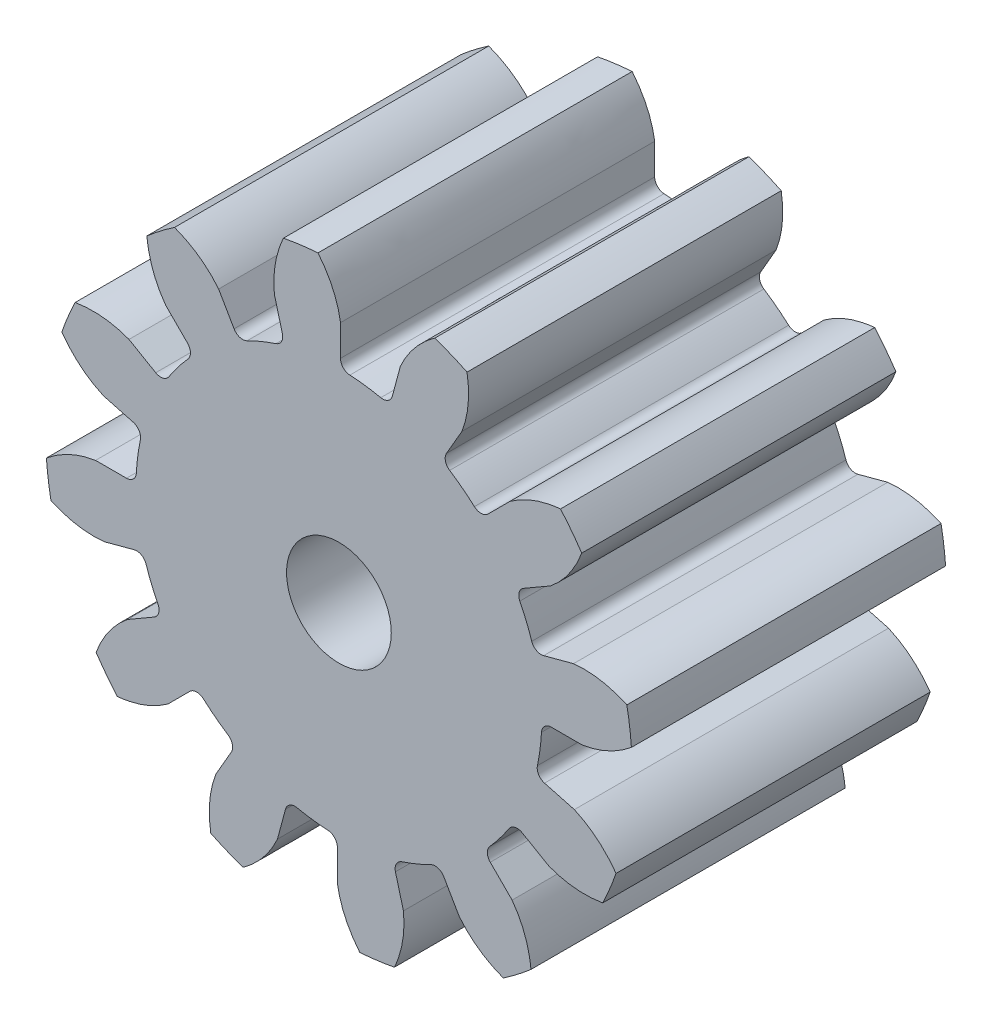
SolidWorks part; units mm, degrees
ref_plane "Front" through (0, 0, 0) normal (0, 0, 1) x (1, 0, 0)
ref_plane "Top" through (0, 0, 0) normal (0, 1, 0) x (1, 0, 0)
ref_plane "Right" through (0, 0, 0) normal (1, 0, 0) x (0, 0, -1)
sketch "Sketch1" plane through (0, 0, 0) normal (0, 0, 1) x (1, 0, 0)
  line L0 (-152.4, 0) -> (152.4, 0) construction
  circle A0 centre (0, 0) radius 8.89
  circle A1 centre (0, 0) radius 7.62 construction
  circle A3 centre (0, 0) radius 6.1506 construction
  dimension "D1" = 1.4694
  dimension "OD" = 17.78
  dimension "Ptich Dia" = 15.24
  dimension "D2" = 2.7394
  dimension "Root Dia" = 12.3012
  dimension "D3" = 1.27
  dimension "Number of Teeth" = 304.8
extrude "Boss-Extrude1" add sketch "Sketch1" against normal blind 9.525
sketch "Sketch3" plane through (0, 0, 0) normal (0, 0, 1) x (1, 0, 0)
  line L0 (0, 0) -> (0, 8.89) construction
  line L1 (-1.8471, 7.1423) -> (0, 7.62)
  line L2 (-9.5921, 7.62) -> (9.5921, 7.62) construction
  line L3 (-9.2865, 5.2183) -> (9.2865, 10.0217) construction
  line L4 (-1.8471, 7.1423) -> (0, 0) construction
  line L5 (-4.563, 5.7968) -> (0, 0) construction
  line L6 (-4.563, 5.7968) -> (-0.6452, 8.8807) construction
  line L7 (-1.288, 7.264) -> (0, 0) construction
  line L8 (-1.288, 7.264) -> (0.027, 7.4971) construction
  arc A0 (-1.8471, 7.1423) -> (-4.563, 5.7968) centre (0, 0) ccw
  circle A1 centre (0, 0) radius 7.62 construction
  circle A2 centre (0, 0) radius 7.3773 construction
  arc A3 (-1.8471, 7.1423) -> (-1.288, 7.264) centre (0, 0) cw
  circle A4 centre (0, 0) radius 8.89 construction
  point P6 (0, 7.62)
  dimension "D1" = 1.9079
  dimension "Pressure Angle" = 14.5
  dimension "D2" = 3.0526
  dimension "D3" = 4.9859
  dimension "D4" = 0.5724
  dimension "D5" = 1.3355
sketch "Sketch4" plane through (0, 0, 0) normal (0, 0, 1) x (1, 0, 0)
  line L0 (0, 0) -> (0.9861, 7.4902) construction
  line L1 (0.0483, 7.3771) -> (0.0483, 6.1504)
  line L2 (0, 7.62) -> (1.9722, 7.3604) construction
  line L3 (1.8627, 7.1383) -> (1.5452, 5.9534)
  line L4 (0.0483, 6.1504) -> (0, 0) construction
  line L5 (0, 0) -> (0, 8.89) construction
  line L6 (-4.563, 5.7968) -> (-0.6452, 8.8807) construction
  line L7 (-4.563, 5.7968) -> (-0.6452, 8.8807) construction
  arc A0 (1.5452, 5.9534) -> (0.0483, 6.1504) centre (0, 0) ccw
  arc A1 (0, 7.62) -> (1.9722, 7.3604) centre (0, 0) cw construction
  circle A2 centre (0, 0) radius 7.62 construction
  circle A3 centre (0, 0) radius 7.3773 construction
  circle A4 centre (0, 0) radius 6.1506 construction
  arc A5 (2.9218, 8.4111) -> (-0.6452, 8.8807) centre (0, 0) ccw
  spline S0 degree 2 poles (-0.6452, 8.8807) (-0.0806, 8.1997) (0.0483, 7.3771) knots 0 0 0 1 1 1
  spline S1 degree 2 poles (2.9218, 8.4111) (2.2001, 7.8994) (1.8627, 7.1383) knots 0 0 0 1 1 1
  dimension "D1" = 1.9949
extrude "Cut-Extrude1" cut sketch "Sketch4" against normal through all
fillet "Fillet1" radius 0.2992 2 edges at (1.5452, 5.9534, -4.7625) (0.0483, 6.1504, -4.7625)
pattern_circular "CirPattern1" count 12 over 360 about axis through (0, 0, -9.525) along (0, 0, 1) of "Cut-Extrude1", "Fillet1"
sketch "Sketch5" plane through (0, 0, 0) normal (0, 0, 1) x (1, 0, 0)
  circle A0 centre (0, 0) radius 1.5875
  circle A1 centre (0, 0) radius 3.9688 construction
  dimension "Bore Min" = 3.175
  dimension "Bore Max" = 7.9375
extrude "Cut-Extrude2" cut sketch "Sketch5" against normal through all
sketch "Pitch Dia" plane through (0, 0, 0) normal (0, 0, 1) x (1, 0, 0)
  circle A0 centre (0, 0) radius 7.62 construction
  circle A1 centre (0, 0) radius 7.62
equation "\"D1@Boss-Extrude1\" = \"Face Wd@Sketch2\""
equation "\"D2@Sketch3\" = \"D1@Sketch3\"*1.6"
equation "\"D3@Sketch3\" = \"D1@Sketch3\"+\"D2@Sketch3\"+.001"
equation "\"D4@Sketch3\" = \"D1@Sketch3\"*.3"
equation "\"D5@Sketch3\" = \"D1@Sketch3\"-\"D4@Sketch3\""
equation "\"D1@Sketch4\" = 1.5708/(\"Number of Teeth@Sketch1\"/\"Ptich Dia@Sketch1\")"
equation "\"D1@Chamfer1\" = \"B Hub Dia@Sketch2\"*.025"
equation "\"D1@CirPattern1\" = \"Number of Teeth@Sketch1\""
equation "\"D1@Fillet1\" = \"D1@Sketch4\"*.15"
equation "\"D1@Fillet2\" = \"OD@Sketch1\"*.01"
equation "\"D1@Sketch1\" = 1.157/(\"Number of Teeth@Sketch1\"/\"Ptich Dia@Sketch1\")"
